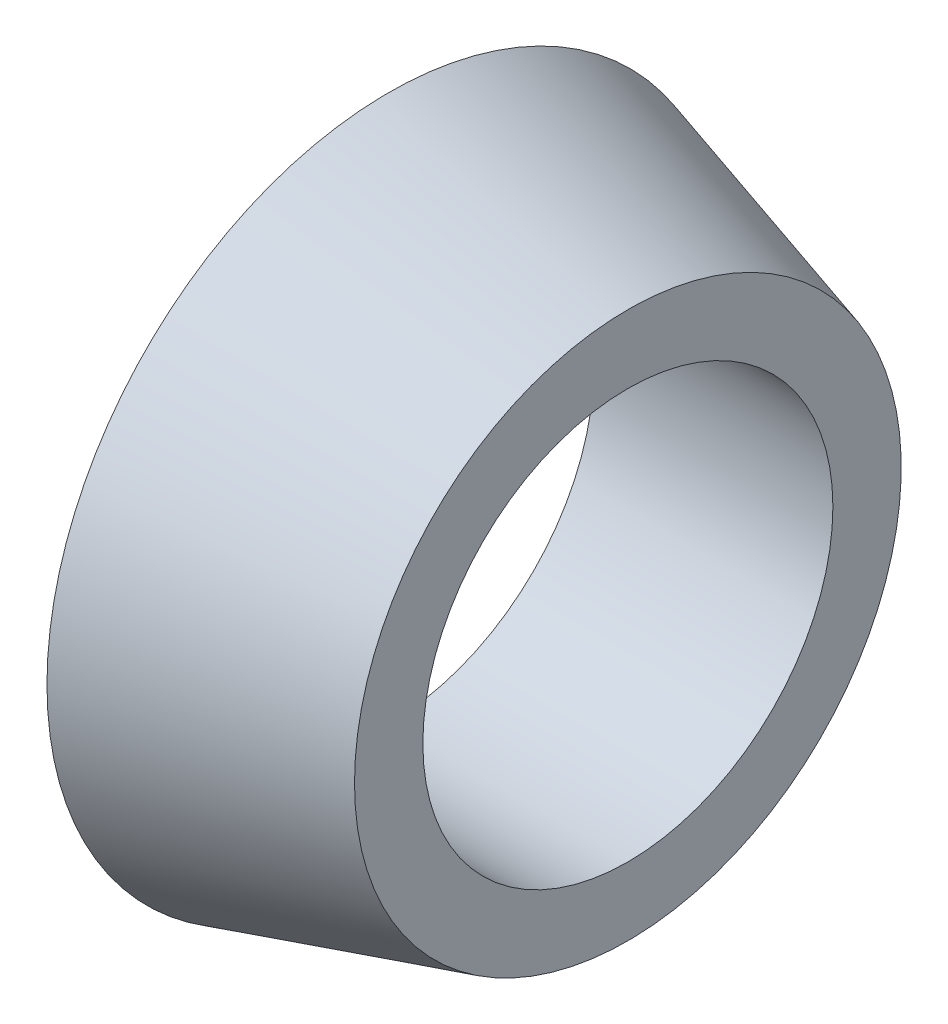
SolidWorks part; units mm, degrees
ref_plane "Płaszczyzna XY" through (0, 0, 0) normal (0, 0, 1) x (1, 0, 0)
ref_plane "Płaszczyzna XZ" through (0, 0, 0) normal (0, 1, 0) x (1, 0, 0)
ref_plane "Płaszczyzna YZ" through (0, 0, 0) normal (1, 0, 0) x (0, 0, -1)
sketch "Szkic1" plane through (0, 0, 0) normal (0, 0, 1) x (1, 0, 0)
  line L0 (0, 6) -> (0, 10)
  line L1 (0, 10) -> (7, 8)
  line L2 (7, 8) -> (7, 6)
  line L3 (7, 6) -> (0, 6)
  line L4 (0, 0) -> (22.8523, 0) construction
  dimension "D1" = 12
  dimension "D2" = 8
  dimension "D3" = 7
  dimension "D4" = 10
revolve "Obrót1" add sketch "Szkic1" angle 360 about L4
